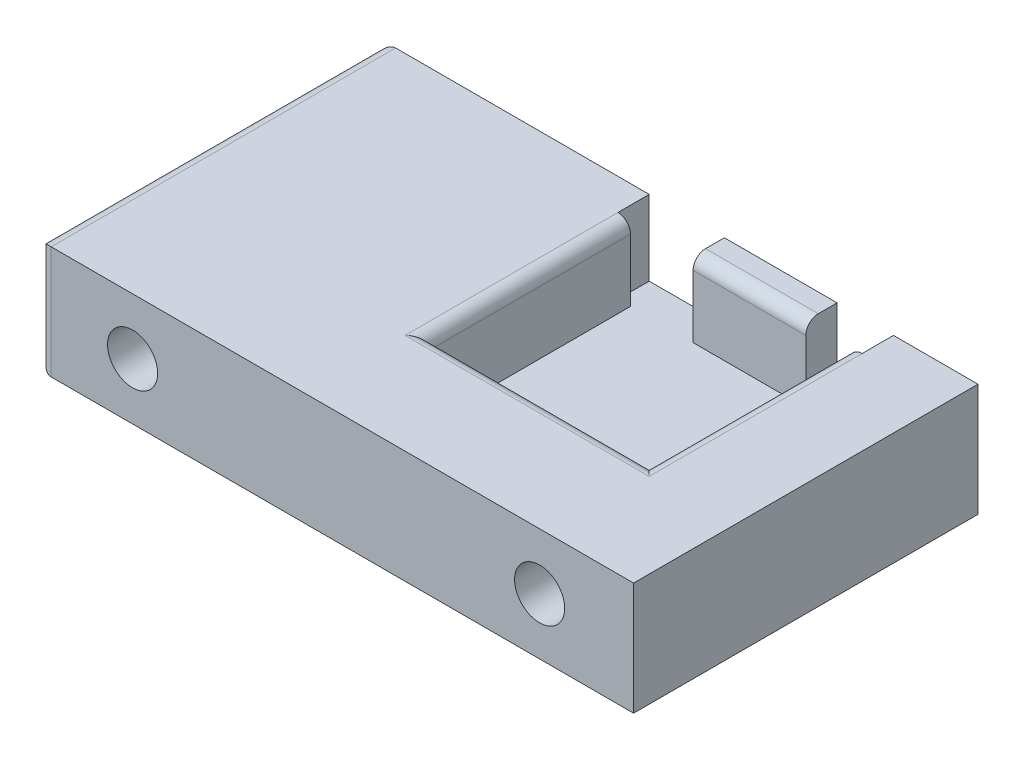
SolidWorks part; units mm, degrees
ref_plane "Front Plane" through (0, 0, 0) normal (0, 0, 1) x (1, 0, 0)
ref_plane "Top Plane" through (0, 0, 0) normal (0, 1, 0) x (1, 0, 0)
ref_plane "Right Plane" through (0, 0, 0) normal (1, 0, 0) x (0, 0, -1)
sketch "Sketch1" plane through (0, 0, 0) normal (0, 1, 0) x (1, 0, 0)
  line L1 (0, 0) -> (95, 0)
  line L2 (0, 0) -> (0, -55)
  line L3 (0, -55) -> (95, -55)
  line L4 (95, 0) -> (95, -55)
  dimension "D1" = 95
  dimension "D2" = 55
extrude "Boss-Extrude1" add sketch "Sketch1" along normal blind 18
sketch "Sketch2" plane through (0, 0, 55) normal (0, 0, 1) x (1, 0, 0)
  line L0 (95, 18) -> (95, 0) construction
  line L1 (0, 0) -> (95, 0) construction
  line L2 (0, 18) -> (0, 0) construction
  circle A0 centre (80, 9) radius 4
  circle A1 centre (15, 9) radius 4
  dimension "D3" = 8
  dimension "D4" = 8
  dimension "D1" = 15
  dimension "D2" = 9
  dimension "D5" = 15
  dimension "D6" = 9
extrude "Cut-Extrude1" cut sketch "Sketch2" against normal blind 15
sketch "Sketch3" plane through (0, 18, 0) normal (0, 1, 0) x (1, 0, 0)
  line L1 (44.5, -5) -> (79.5, -5)
  line L2 (44.5, -5) -> (44.5, -37)
  line L3 (44.5, -37) -> (79.5, -37)
  line L4 (79.5, -5) -> (79.5, -37)
  line L5 (95, 0) -> (0, 0) construction
  dimension "D1" = 35
  dimension "D2" = 32
  dimension "D3" = 5
extrude "Cut-Extrude2" cut sketch "Sketch3" against normal blind 12
fillet "Fillet2" radius 2 8 edges at (0, 9, 0) (0, 18, 27.5) (0, 0, 27.5) (0, 9, 55) (79.5, 18, 21) (62, 18, 5) (44.5, 18, 21) (62, 18, 37)
sketch "Sketch4" plane through (0, 18, 0) normal (0, 1, 0) x (1, 0, 0)
  line L0 (95, 0) -> (2, 0) construction
  line L1 (42.5, 0) -> (54.5, 0)
  line L2 (42.5, 0) -> (42.5, -5)
  line L3 (42.5, -5) -> (54.5, -5)
  line L4 (54.5, 0) -> (54.5, -5)
  line L5 (79.5, -5) -> (44.5, -5) construction
  dimension "D1" = 5
  dimension "D2" = 12
extrude "Cut-Extrude3" cut sketch "Sketch4" against normal blind 12
sketch "Sketch5" plane through (0, 18, 0) normal (0, 1, 0) x (1, 0, 0)
  line L13 (95, 0) -> (54.5, 0) construction
  line L14 (72.5, 0) -> (81.5, 0)
  line L15 (72.5, 0) -> (72.5, -5)
  line L16 (72.5, -5) -> (81.5, -5)
  line L17 (81.5, 0) -> (81.5, -5)
  line L18 (81.5, -3) -> (81.5, -39) construction
  dimension "D1" = 9
  dimension "D2" = 5
extrude "Cut-Extrude4" cut sketch "Sketch5" against normal blind 12
